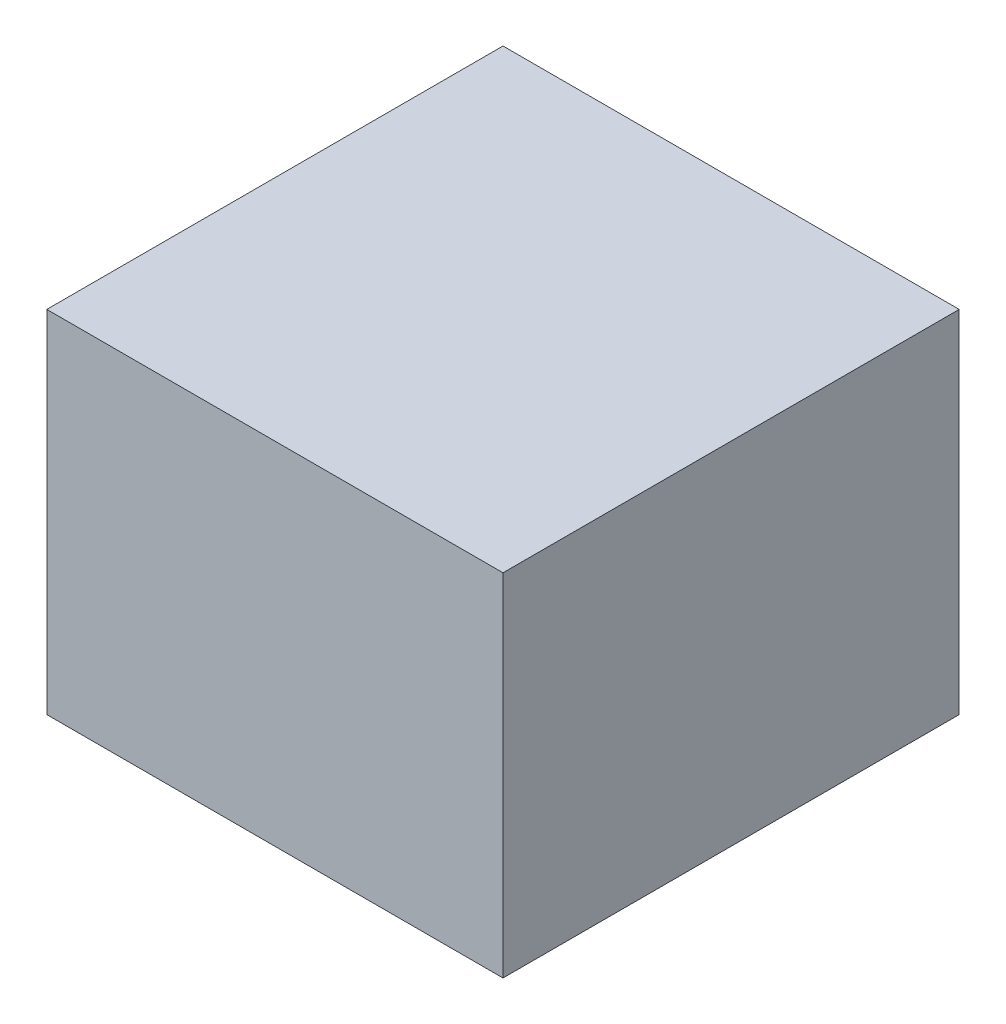
SolidWorks part; units mm, degrees
material "1060 Alloy"
ref_plane "Front Plane" through (0, 0, 0) normal (0, 0, 1) x (1, 0, 0)
ref_plane "Top Plane" through (0, 0, 0) normal (0, 1, 0) x (1, 0, 0)
ref_plane "Right Plane" through (0, 0, 0) normal (1, 0, 0) x (0, 0, -1)
sketch "Sketch1" plane through (0, 0, 0) normal (0, 1, 0) x (1, 0, 0)
  line L1 (-22.5, 22.5) -> (22.5, 22.5)
  line L2 (-22.5, 22.5) -> (-22.5, -22.5)
  line L3 (-22.5, -22.5) -> (22.5, -22.5)
  line L4 (22.5, 22.5) -> (22.5, -22.5)
  line L5 (-22.5, 22.5) -> (22.5, -22.5) construction
  line L6 (-22.5, -22.5) -> (22.5, 22.5) construction
  point P0 (0, 0)
  dimension "D1" = 45
  dimension "D2" = 45
extrude "Boss-Extrude1" add sketch "Sketch1" along normal blind 7.5
sketch "Sketch2" plane through (0, 7.5, 0) normal (0, 1, 0) x (1, 0, 0)
  line L0 (22.5, -22.5) -> (22.5, 22.5) construction
  line L1 (-32.5, 32.5) -> (32.5, 32.5)
  line L2 (-32.5, 32.5) -> (-32.5, -32.5)
  line L3 (-32.5, -32.5) -> (32.5, -32.5)
  line L4 (32.5, 32.5) -> (32.5, -32.5)
  line L5 (-32.5, 32.5) -> (32.5, -32.5) construction
  line L6 (-32.5, -32.5) -> (32.5, 32.5) construction
  line L7 (-22.5, -22.5) -> (22.5, -22.5) construction
  point P0 (0, 0)
  dimension "D1" = 10
  dimension "D2" = 10
extrude "Boss-Extrude2" add sketch "Sketch2" along normal blind 50
